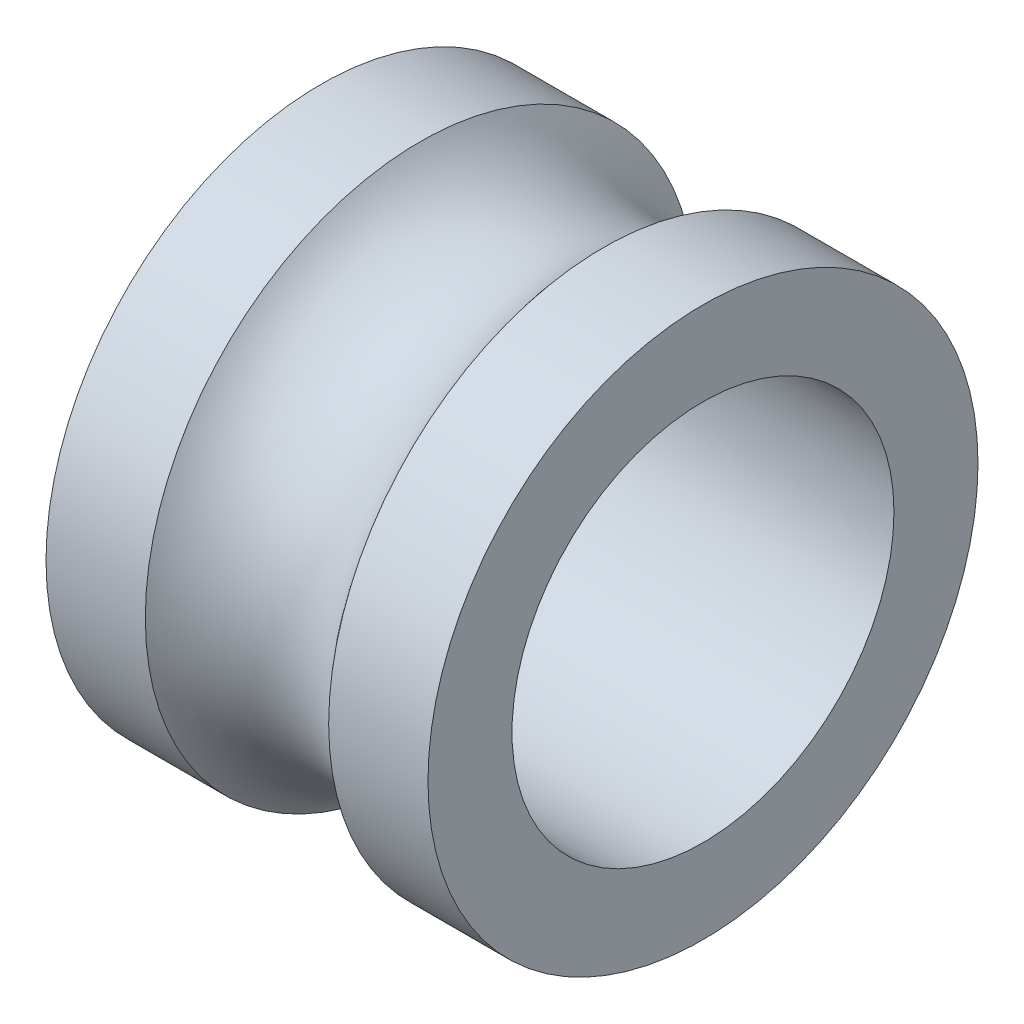
SolidWorks part; units mm, degrees
ref_plane "Ön Düzlem" through (0, 0, 0) normal (0, 0, 1) x (1, 0, 0)
ref_plane "Üst Düzlem" through (0, 0, 0) normal (0, 1, 0) x (1, 0, 0)
ref_plane "Sağ Düzlem" through (0, 0, 0) normal (1, 0, 0) x (0, 0, -1)
sketch "Çizim1" plane through (0, 0, 0) normal (0, 0, 1) x (1, 0, 0)
  line L0 (2.5, 2.5) -> (-2.5, 2.5)
  line L1 (-2.5, 2.5) -> (-2.5, 3.6)
  line L2 (-2.5, 3.6) -> (-1.2, 3.6)
  line L3 (2.5, 3.6) -> (2.5, 2.5)
  line L4 (0, 0) -> (-59.7632, 0) construction
  line L5 (1.2, 3.6) -> (2.5, 3.6)
  arc A0 (1.2, 3.6) -> (-1.2, 3.6) centre (0, 4.5) cw
  point P2 (0, 2.5)
  point P10 (0, 3)
  dimension "D4" = 1.5
  dimension "D1" = 2.5
  dimension "D2" = 5
  dimension "D3" = 1.1
  dimension "D5" = 0.6
revolve "Döndür1" add sketch "Çizim1" angle 360 about L4
